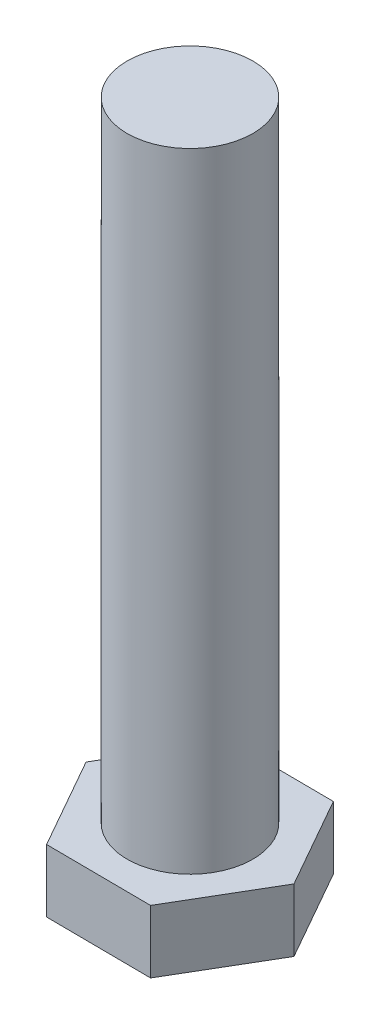
SolidWorks part; units mm, degrees
ref_plane "Front Plane" through (0, 0, 0) normal (0, 0, 1) x (1, 0, 0)
ref_plane "Top Plane" through (0, 0, 0) normal (0, 1, 0) x (1, 0, 0)
ref_plane "Right Plane" through (0, 0, 0) normal (1, 0, 0) x (0, 0, -1)
sketch "Sketch1" plane through (0, 0, 0) normal (0, 1, 0) x (1, 0, 0)
  circle A0 centre (0, 0) radius 1.5
  dimension "D1" = 3
extrude "Boss-Extrude1" add sketch "Sketch1" along normal blind 15
sketch "Sketch2" plane through (0, 0, 0) normal (0, -1, 0) x (1, 0, 0)
  line L1 (2.5, 0.0189) -> (1.2336, 2.1745)
  line L2 (1.2336, 2.1745) -> (-1.2664, 2.1556)
  line L3 (-1.2664, 2.1556) -> (-2.5, -0.0189)
  line L4 (-2.5, -0.0189) -> (-1.2336, -2.1745)
  line L5 (-1.2336, -2.1745) -> (1.2664, -2.1556)
  line L6 (1.2664, -2.1556) -> (2.5, 0.0189)
  circle A0 centre (0, 0) radius 2.1651 construction
  dimension "D1" = 2.5
extrude "Boss-Extrude2" add sketch "Sketch2" along normal blind 1.5
equation "\"thread_dist\"= 3.5"
equation "\"thread_diameter\"= 3"
equation "\"D13@Sketch1\"=\"thread_diameter\""
equation "\"D14@Sketch1\"=\"thread_dist\""
equation "\"D11@Sketch1\"=\"thread_diameter\""
equation "\"D12@Sketch1\"=\"thread_dist\""
equation "\"D8@Sketch1\"=\"thread_diameter\""
equation "\"D10@Sketch1\"=\"thread_dist\""
equation "\"D1@Sketch1\"=\"thread_diameter\""
equation "\"thread_length\"=15"
equation "\"D1@Boss-Extrude1\"=\"thread_length\""
